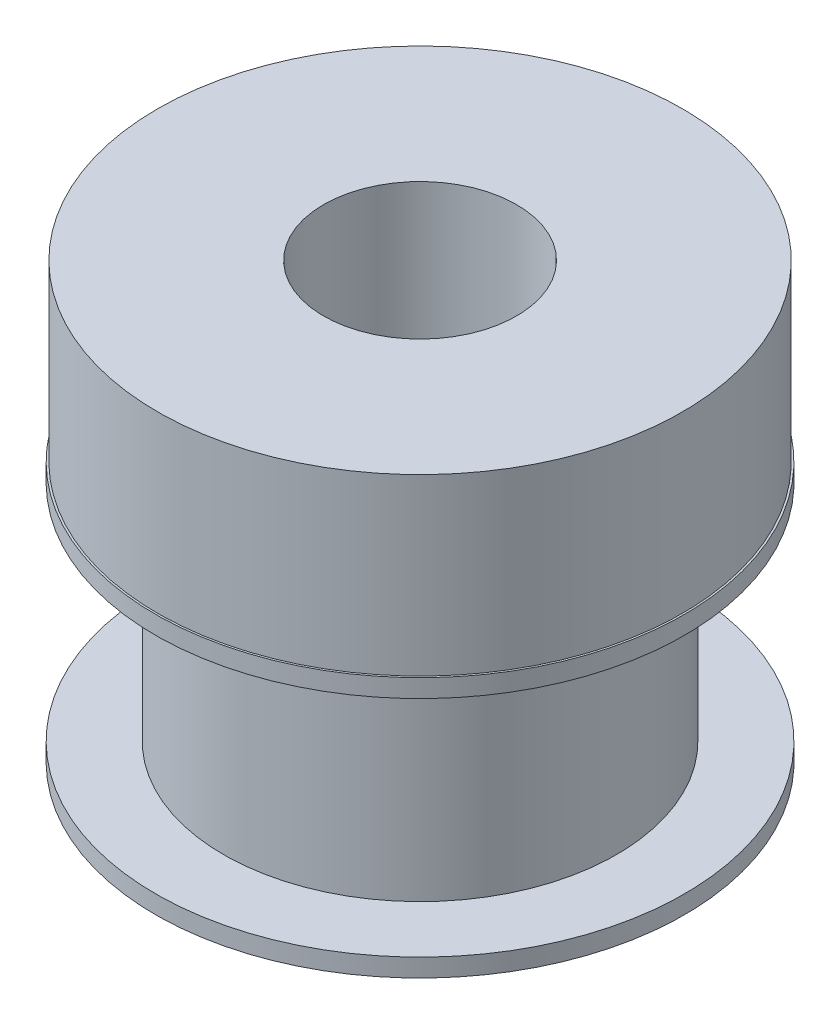
SolidWorks part; units mm, degrees
material "6061 Alloy"
ref_plane "Front Plane" through (0, 0, 0) normal (0, 0, 1) x (1, 0, 0)
ref_plane "Top Plane" through (0, 0, 0) normal (0, 1, 0) x (1, 0, 0)
ref_plane "Right Plane" through (0, 0, 0) normal (1, 0, 0) x (0, 0, -1)
sketch "Sketch1" plane through (0, 0, 0) normal (0, 0, 1) x (1, 0, 0)
  line L0 (0, 26.6826) -> (0, -24.1064) construction
  line L1 (6.4643, 0.5969) -> (6.4643, 7.9629)
  line L2 (6.4643, 7.9629) -> (8.6995, 7.9629)
  line L3 (8.6995, 7.9629) -> (8.6995, 8.5598)
  line L4 (8.6995, 8.5598) -> (8.636, 8.5598)
  line L5 (8.636, 8.5598) -> (8.636, 14.3002)
  line L6 (8.636, 14.3002) -> (3.175, 14.3002)
  line L7 (3.175, 14.3002) -> (3.175, 0)
  line L8 (3.175, 0) -> (8.6995, 0)
  line L9 (8.6995, 0) -> (8.6995, 0.5969)
  line L10 (8.6995, 0.5969) -> (6.4643, 0.5969)
  dimension "D1" = 17.399
  dimension "D2" = 6.35
  dimension "D3" = 12.9286
  dimension "D4" = 7.366
  dimension "D5" = 8.5598
  dimension "D6" = 14.3002
  dimension "D7" = 17.272
revolve "Revolve1" add sketch "Sketch1" angle 360 about L0
